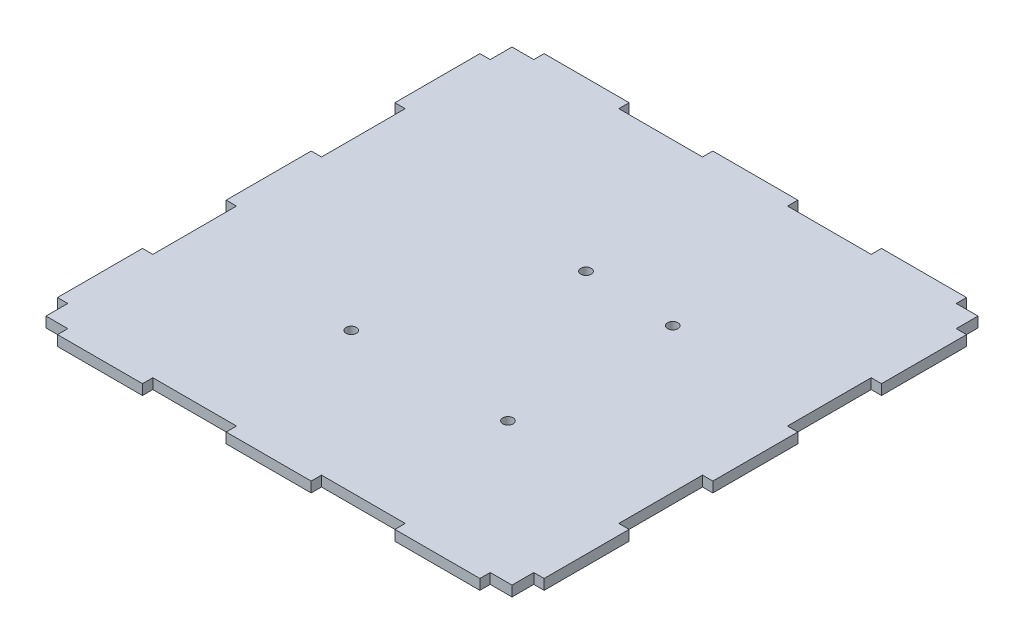
SolidWorks part; units mm, degrees
ref_plane "Front Plane" through (0, 0, 0) normal (0, 0, 1) x (1, 0, 0)
ref_plane "Top Plane" through (0, 0, 0) normal (0, 1, 0) x (1, 0, 0)
ref_plane "Right Plane" through (0, 0, 0) normal (1, 0, 0) x (0, 0, -1)
sketch "Sketch1" plane through (0, 0, 0) normal (0, 1, 0) x (1, 0, 0)
  line L5 (-75, 75) -> (75, 75)
  line L6 (-75, 75) -> (-75, -75)
  line L7 (-75, -75) -> (75, -75)
  line L8 (75, 75) -> (75, -75)
  line L9 (-75, 75) -> (75, -75) construction
  line L10 (-75, -75) -> (75, 75) construction
  point P0 (0, 0)
  dimension "D1" = 150
extrude "Boss-Extrude1" add sketch "Sketch1" along normal blind 3.18
sketch "Sketch5" plane through (0, 0, 0) normal (0, -1, 0) x (1, 0, 0)
  line L1 (-12.25, -33.75) -> (12.25, -33.75)
  line L2 (-12.25, -33.75) -> (-12.25, 33.75)
  line L3 (-12.25, 33.75) -> (12.25, 33.75)
  line L4 (12.25, -33.75) -> (12.25, 33.75)
  line L5 (-12.25, -33.75) -> (12.25, 33.75) construction
  line L6 (-12.25, 33.75) -> (12.25, -33.75) construction
  point P0 (0, 0)
  dimension "D1" = 67.5
  dimension "D2" = 24.5
extrude "Cut-Extrude4" [suppressed] cut sketch "Sketch5" against normal blind 3.18
sketch "Sketch9" plane through (0, 0, 0) normal (0, -1, 0) x (1, 0, 0)
  line L0 (75, 75) -> (75, -75) construction
  line L1 (75, 75) -> (71.82, 75)
  line L2 (75, 75) -> (75, 65.1)
  line L3 (75, 65.1) -> (71.82, 65.1)
  line L4 (71.82, 75) -> (71.82, 65.1)
  line L5 (75, 38.9) -> (71.82, 38.9)
  line L6 (75, 38.9) -> (75, 13.1)
  line L7 (75, 13.1) -> (71.82, 13.1)
  line L8 (71.82, 38.9) -> (71.82, 13.1)
  dimension "D1" = 9.9
  dimension "D2" = 3.18
  dimension "D3" = 25.8
  dimension "D4" = 3.18
  dimension "D5" = 26.2
extrude "Cut-Extrude7" cut sketch "Sketch9" against normal blind 10
mirror "Mirror1" about plane through (0, 0, 0) normal (0, 0, 1) of "Cut-Extrude7"
mirror "Mirror2" about plane through (0, 0, 0) normal (1, 0, 0) of "Mirror1", "Cut-Extrude7"
sketch "Sketch10" plane through (0, 0, 0) normal (0, -1, 0) x (1, 0, 0)
  line L0 (-71.82, 75) -> (71.82, 75) construction
  line L1 (71.82, 75) -> (65.1, 75)
  line L2 (71.82, 75) -> (71.82, 71.82)
  line L3 (71.82, 71.82) -> (65.1, 71.82)
  line L4 (65.1, 75) -> (65.1, 71.82)
  line L5 (38.9, 75) -> (13.1, 75)
  line L6 (38.9, 75) -> (38.9, 71.82)
  line L7 (38.9, 71.82) -> (13.1, 71.82)
  line L8 (13.1, 75) -> (13.1, 71.82)
  point P11 (65.1, 73.41)
  dimension "D1" = 6.72
  dimension "D2" = 3.18
  dimension "D3" = 3.18
  dimension "D4" = 25.8
  dimension "D5" = 26.2
extrude "Cut-Extrude8" cut sketch "Sketch10" against normal blind 10
mirror "Mirror4" about plane through (0, 0, 0) normal (1, 0, 0) of "Cut-Extrude8"
mirror "Mirror5" about plane through (0, 0, 0) normal (0, 0, 1) of "Mirror4", "Cut-Extrude8"
sketch "Sketch11" plane through (0, 0, 0) normal (0, -1, 0) x (1, 0, 0)
  line L0 (75, 65.1) -> (75, 38.9) construction
  line L1 (38.9, 75) -> (65.1, 75) construction
  circle A0 centre (27.35, 28.6) radius 1.6
  dimension "D1" = 3.2
  dimension "D3" = 46.4
  dimension "D2" = 47.65
extrude "Cut-Extrude9" cut sketch "Sketch11" against normal blind 10
sketch "Sketch12" plane through (0, 0, 0) normal (0, -1, 0) x (1, 0, 0)
  line L0 (-65.1, 75) -> (-38.9, 75) construction
  circle A0 centre (-20.95, 28.6) radius 1.6
  circle A1 centre (27.35, 28.6) radius 1.6 construction
  dimension "D1" = 3.2
  dimension "D2" = 48.3
  dimension "D3" = 46.4
extrude "Cut-Extrude10" cut sketch "Sketch12" against normal blind 10
sketch "Sketch13" plane through (0, 0, 0) normal (0, -1, 0) x (1, 0, 0)
  line L0 (75, -38.9) -> (75, -65.1) construction
  circle A0 centre (27.35, -22.2) radius 1.6
  circle A1 centre (27.35, 28.6) radius 1.6 construction
  dimension "D1" = 3.2
  dimension "D2" = 50.8
  dimension "D3" = 47.65
extrude "Cut-Extrude11" cut sketch "Sketch13" against normal blind 10
sketch "Sketch14" plane through (0, 0, 0) normal (0, -1, 0) x (1, 0, 0)
  line L0 (13.1, -75) -> (-13.1, -75) construction
  circle A0 centre (-0.55, -23.3605) radius 1.6
  circle A1 centre (27.35, -22.2) radius 1.6 construction
  dimension "D1" = 3.2
  dimension "D2" = 27.9
  dimension "D3" = 51.6395
extrude "Cut-Extrude12" cut sketch "Sketch14" against normal blind 10
sketch "Sketch15" [suppressed] plane through (0, 0, 0) normal (0, -1, 0) x (-1, 0, 0)
  line L0 (12.25, 33.75) -> (-12.25, 33.75) construction
  line L1 (-12.25, 33.75) -> (-12.25, -33.75) construction
  circle A0 centre (-18.75, 40.25) radius 0.945
  dimension "D1" = 1.89
  dimension "D2" = 6.5
  dimension "D3" = 6.5
extrude "Cut-Extrude13" [suppressed] cut sketch "Sketch15" against normal blind 10
sketch "Sketch16" [suppressed] plane through (0, 0, 0) normal (0, -1, 0) x (1, 0, 0)
  line L0 (-12.25, 33.75) -> (-12.25, -33.75) construction
  line L1 (-12.25, -33.75) -> (12.25, -33.75) construction
  circle A0 centre (-18.75, -40.25) radius 0.945
  dimension "D1" = 1.89
  dimension "D2" = 6.5
  dimension "D3" = 6.5
extrude "Cut-Extrude14" [suppressed] cut sketch "Sketch16" against normal blind 10
sketch "Sketch17" [suppressed] plane through (0, 0, 0) normal (0, -1, 0) x (1, 0, 0)
  line L0 (12.25, -33.75) -> (12.25, 33.75) construction
  line L1 (12.25, 33.75) -> (-12.25, 33.75) construction
  circle A0 centre (18.75, 40.25) radius 0.945
  dimension "D1" = 1.89
  dimension "D2" = 6.5
  dimension "D3" = 6.5
extrude "Cut-Extrude15" [suppressed] cut sketch "Sketch17" against normal blind 10
sketch "Sketch18" [suppressed] plane through (0, 0, 0) normal (0, -1, 0) x (1, 0, 0)
  line L0 (-12.25, 33.75) -> (-12.25, -33.75) construction
  line L1 (12.25, 33.75) -> (-12.25, 33.75) construction
  circle A0 centre (-18.75, 40.25) radius 0.945
  dimension "D1" = 1.89
  dimension "D2" = 6.5
  dimension "D3" = 6.5
extrude "Cut-Extrude16" [suppressed] cut sketch "Sketch18" against normal blind 10
sketch "Sketch19" [suppressed] plane through (0, 0, 0) normal (0, -1, 0) x (1, 0, 0)
  line L0 (0, 0) -> (-58.7417, 0) construction
  line L1 (-12.25, 33.75) -> (-12.25, -33.75) construction
  circle A0 centre (-32.25, 15) radius 3.5
  dimension "D1" = 7
  dimension "D2" = 15
  dimension "D3" = 20
extrude "Cut-Extrude17" [suppressed] cut sketch "Sketch19" against normal blind 10
sketch "Sketch20" [suppressed] plane through (0, 0, 0) normal (0, -1, 0) x (1, 0, 0)
  line L0 (0, 0) -> (-54.6239, 0) construction
  line L1 (-12.25, 33.75) -> (-12.25, -33.75) construction
  circle A0 centre (-32.25, -15) radius 3.18
  dimension "D1" = 6.36
  dimension "D2" = 15
  dimension "D3" = 20
extrude "Cut-Extrude18" [suppressed] cut sketch "Sketch20" against normal blind 10
sketch "Sketch21" [suppressed] plane through (0, 0, 0) normal (0, -1, 0) x (1, 0, 0)
  line L0 (-32.25, 15) -> (-32.25, 39.4432) construction
  line L2 (-33.75, 23.5) -> (-30.75, 23.5)
  line L3 (-33.75, 23.5) -> (-33.75, 22.5)
  line L4 (-33.75, 22.5) -> (-30.75, 22.5)
  line L5 (-30.75, 23.5) -> (-30.75, 22.5)
  line L6 (-33.75, 23.5) -> (-30.75, 22.5) construction
  line L7 (-33.75, 22.5) -> (-30.75, 23.5) construction
  circle A0 centre (-32.25, 15) radius 3.5 construction
  point P3 (-32.25, 23)
  dimension "D1" = 1
  dimension "D2" = 3
  dimension "D3" = 7.5
extrude "Cut-Extrude19" [suppressed] cut sketch "Sketch21" against normal blind 10
